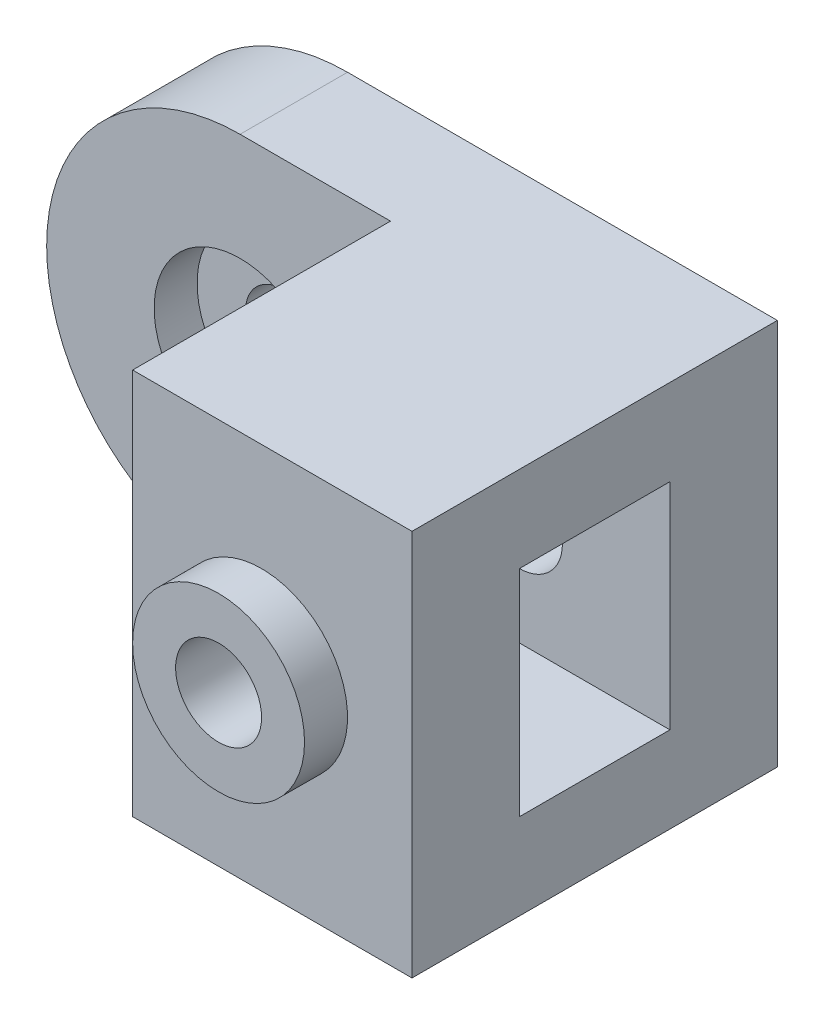
SolidWorks part; units mm, degrees
ref_plane "Front Plane" through (0, 0, 0) normal (0, 0, 1) x (1, 0, 0)
ref_plane "Top Plane" through (0, 0, 0) normal (0, 1, 0) x (1, 0, 0)
ref_plane "Right Plane" through (0, 0, 0) normal (1, 0, 0) x (0, 0, -1)
sketch "Sketch1" plane through (0, 0, 0) normal (0, 0, 1) x (1, 0, 0)
  line L1 (0, 0) -> (145, 0)
  line L2 (0, 0) -> (0, 90)
  line L3 (0, 90) -> (145, 90)
  line L4 (145, 0) -> (145, 90)
  dimension "D1" = 90
  dimension "D2" = 145
extrude "Boss-Extrude1" add sketch "Sketch1" along normal blind 85
sketch "Sketch2" plane through (0, 0, 85) normal (0, 0, 1) x (1, 0, 0)
  line L0 (145, 90) -> (0, 90) construction
  line L1 (45, 90) -> (0, 90)
  line L2 (0, 90) -> (0, 0)
  line L3 (0, 0) -> (45, 0)
  arc A0 (45, 90) -> (45, 0) centre (45, 45) ccw
  line M1 (0, 90) -> (0, 0)
  line M2 (0, 0) -> (145, 0)
  line M4 (145, 90) -> (0, 90)
  dimension "D2" = 45
  dimension "D1" = 45
  dimension "D3" = 45
  dimension "D4" = 45
  dimension "D5" = 90
extrude "Cut-Extrude1" cut sketch "Sketch2" against normal blind 85 contours A0 M4 M1 | A0 L2 M2
sketch "Sketch4" plane through (0, 0, 85) normal (0, 0, 1) x (1, 0, 0)
  line L0 (80, 90) -> (80, 0)
  line L1 (145, 90) -> (45, 90) construction
  line L2 (45, 0) -> (145, 0) construction
  line L3 (80, 0) -> (45, 0)
  line L4 (45, 90) -> (80, 90)
  arc A0 (45, 90) -> (45, 0) centre (45, 45) ccw
  arc M1 (45, 90) -> (45, 0) centre (45, 45) ccw
  line M2 (45, 0) -> (145, 0)
  line M4 (145, 90) -> (45, 90)
  dimension "D1" = 35
extrude "Cut-Extrude3" cut sketch "Sketch4" against normal blind 50 contours L0 M4 M1 M2
sketch "Sketch5" plane through (0, 0, 35) normal (0, 0, 1) x (1, 0, 0)
  point P0 (45, 45)
  point P1 (110, 45)
  dimension "D1" = 35
  dimension "D2" = 45
hole_wizard "M20 Tapped Hole1" positions "3DSketch1" profile "Sketch6" tap size "M20" standard "ISO"
sketch3d "3DSketch1"
  point P0 (45, 45, 35)
  point P3 (110, 45, 35)
sketch "Sketch6" plane through (45, 45, 35) normal (1, 0, 0) x (0, -1, 0)
  line L0 (0, 0) -> (0, 45.2575)
  line L1 (0, 45.2575) -> (8.75, 40)
  line L2 (8.75, 40) -> (8.75, 0)
  line L5 (8.75, 0) -> (0, 0)
  line L10 (0, 45.2575) -> (-8.75, 40) construction
  line L11 (0, -6.35) -> (0, 107.95) construction
  dimension "Tap Drill Dia." = 17.5
  dimension "Tap Drill Depth" = 40
  dimension "Drill Angle" = 118
cosmetic thread "Hole Thread1" parameters "D1"=20, "D2"=20
cosmetic thread "Hole Thread2" parameters "D1"=20, "D2"=20
sketch "Sketch8" plane through (0, 0, 85) normal (0, 0, 1) x (1, 0, 0)
  point P0 (110, 45)
  dimension "D1" = 35
  dimension "D2" = 45
hole_wizard "M20 Tapped Hole3" positions "3DSketch5" profile "Sketch11" tap size "M20" standard "ISO"
sketch3d "3DSketch5"
  point P0 (110, 45, 85)
sketch "Sketch11" plane through (110, 45, 85) normal (1, 0, 0) x (0, -1, 0)
  line L0 (0, 0) -> (0, 65.2575)
  line L1 (0, 65.2575) -> (8.75, 60)
  line L2 (8.75, 60) -> (8.75, 0)
  line L5 (8.75, 0) -> (0, 0)
  line L10 (0, 65.2575) -> (-8.75, 60) construction
  line L11 (0, -6.35) -> (0, 107.95) construction
  dimension "Tap Drill Dia." = 17.5
  dimension "Tap Drill Depth" = 60
  dimension "Drill Angle" = 118
cosmetic thread "Hole Thread4" parameters "D1"=60, "D2"=20
sketch "Sketch12" plane through (0, 0, 35) normal (0, 0, 1) x (1, 0, 0)
  circle A0 centre (45, 45) radius 10
  circle A1 centre (45, 45) radius 20
  dimension "D1" = 20
  dimension "D2" = 40
extrude "Cut-Extrude4" cut sketch "Sketch12" against normal blind 10
sketch "Sketch13" plane through (0, 0, 35) normal (0, 0, 1) x (1, 0, 0)
  circle A0 centre (45, 45) radius 8.75
  circle A1 centre (45, 45) radius 10
  dimension "D1" = 17.5
  dimension "D2" = 20
extrude "Cut-Extrude5" cut sketch "Sketch13" against normal blind 10
sketch "Sketch14" plane through (0, 0, 35) normal (0, 0, 1) x (1, 0, 0)
  line L0 (80, 90) -> (80, 0)
  line L1 (80, 0) -> (45, 0)
  line L2 (45, 90) -> (80, 90)
  arc A0 (45, 90) -> (45, 0) centre (45, 45) ccw
  arc A1 (45, 90) -> (45, 0) centre (45, 45) ccw construction
extrude "Cut-Extrude6" cut sketch "Sketch14" against normal blind 10
sketch "Sketch15" plane through (0, 0, 25) normal (0, 0, 1) x (1, 0, 0)
  circle A1 centre (45, 45) radius 20
  circle A2 centre (45, 45) radius 10
  dimension "D1" = 40
  dimension "D2" = 20
extrude "Cut-Extrude7" cut sketch "Sketch15" against normal blind 10
sketch "Sketch16" plane through (0, 0, 25) normal (0, 0, 1) x (1, 0, 0)
  circle A0 centre (45, 45) radius 8.75
  circle A1 centre (45, 45) radius 10
  dimension "D1" = 17.5
  dimension "D2" = 20
extrude "Cut-Extrude8" cut sketch "Sketch16" against normal blind 10
sketch "Sketch17" plane through (80, 0, 0) normal (-1, 0, 0) x (0, 0, 1)
  line L0 (25, 0) -> (25, 90) construction
  line L1 (25, 70) -> (60, 70)
  line L2 (25, 70) -> (25, 20)
  line L3 (25, 20) -> (60, 20)
  line L4 (60, 70) -> (60, 20)
  dimension "D1" = 35
  dimension "D2" = 20
  dimension "D3" = 50
extrude "Cut-Extrude9" cut sketch "Sketch17" against normal blind 97
sketch "Sketch18" plane through (0, 0, 85) normal (0, 0, 1) x (1, 0, 0)
  circle A0 centre (110, 45) radius 10
  circle A1 centre (110, 45) radius 20
  dimension "D1" = 20
  dimension "D2" = 40
extrude "Boss-Extrude2" add sketch "Sketch18" along normal blind 10
sketch "Sketch19" plane through (0, 0, 60) normal (0, 0, -1) x (-1, 0, 0)
  circle A0 centre (-110, 45) radius 8.75
  circle A1 centre (-110, 45) radius 20
  dimension "D1" = 17.5
  dimension "D2" = 40
extrude "Boss-Extrude3" add sketch "Sketch19" along normal blind 10
sketch "Sketch20" plane through (0, 0, 85) normal (0, 0, 1) x (1, 0, 0)
  circle A0 centre (110, 45) radius 8.75
  circle A1 centre (110, 45) radius 10
  dimension "D1" = 17.5
  dimension "D2" = 20
extrude "Cut-Extrude10" cut sketch "Sketch20" against normal blind 120
equation "\"A\"=10"
